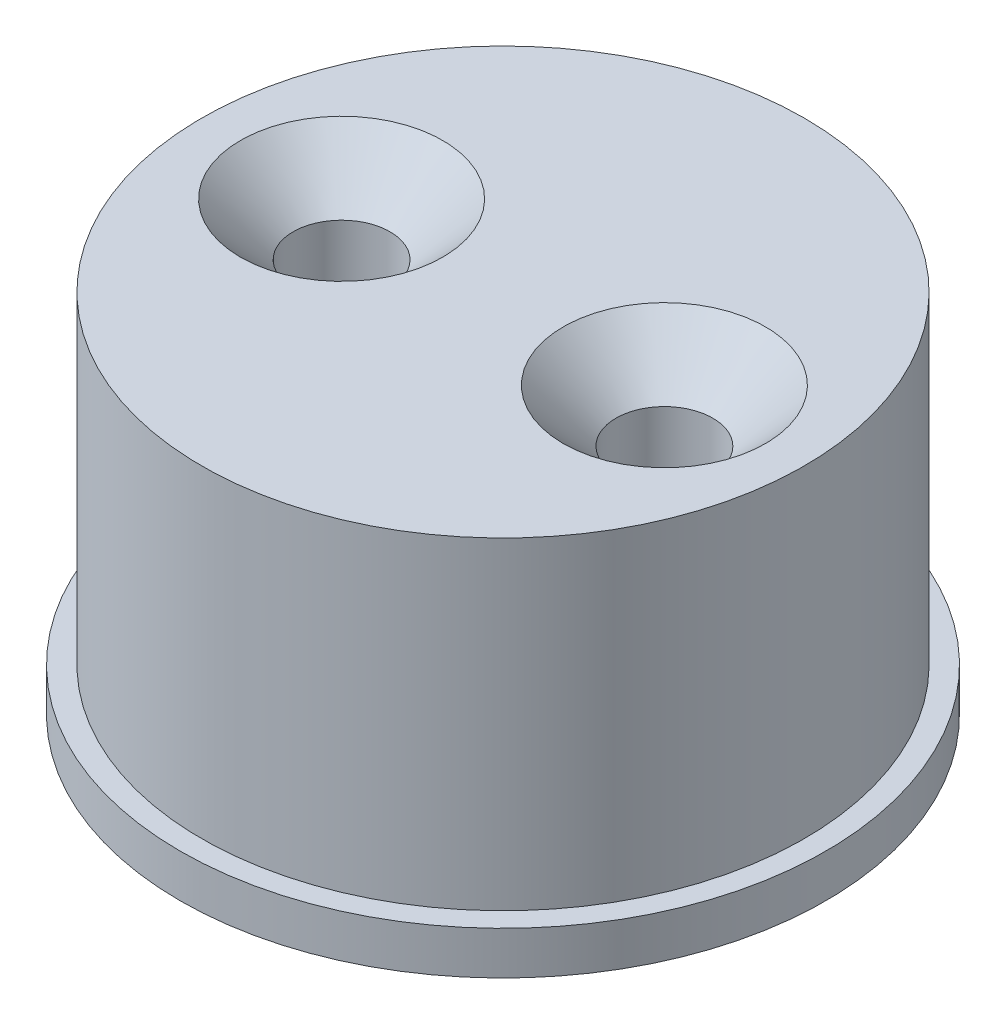
SolidWorks part; units mm, degrees
material "AISI 304"
ref_plane "정면" through (0, 0, 0) normal (0, 0, 1) x (1, 0, 0)
ref_plane "윗면" through (0, 0, 0) normal (0, 1, 0) x (1, 0, 0)
ref_plane "우측면" through (0, 0, 0) normal (1, 0, 0) x (0, 0, -1)
sketch "스케치1" plane through (0, 0, 0) normal (0, 0, 1) x (1, 0, 0)
  line L0 (0, 0) -> (0, 23.922) construction
  line L1 (0, 0) -> (-15, 0)
  line L2 (-15, 0) -> (-15, 2)
  line L3 (-15, 2) -> (-14, 2)
  line L4 (-14, 2) -> (-14, 17)
  line L5 (-14, 17) -> (0, 17)
  line L6 (0, 17) -> (0, 0)
  dimension "D1" = 30
  dimension "D2" = 28
  dimension "D3" = 2
  dimension "D4" = 15
revolve "회전1" add sketch "스케치1" angle 360 about L0
hole_wizard "M4 접시 머리 나사용 카운터싱크1" positions "스케치2" profile "스케치3" countersink size "M4" standard "ISO" end condition up to next
sketch "스케치2" plane through (0, 17, 0) normal (0, 1, 0) x (1, 0, 0)
  line L0 (-7.5, 0) -> (7.5, 0)
  circle A0 centre (0, 0) radius 14 construction
  point P0 (-7.5, 0)
  point P2 (7.5, 0)
  point P10 (0, 0)
  dimension "D1" = 15
sketch "스케치3" plane through (-7.5, 17, 0) normal (1, 0, 0) x (0, 0, 1)
  line L0 (0, 0) -> (0, 17)
  line L1 (0, 17) -> (2.25, 17)
  line L2 (2.25, 17) -> (2.25, 2.45)
  line L3 (2.25, 2.45) -> (4.7, 0)
  line L5 (4.7, 0) -> (0, 0)
  line L6 (-2.25, 2.45) -> (-4.7, 0) construction
  line L11 (0, -6.35) -> (0, 107.95) construction
  dimension "관통 구멍 지름" = 4.5
  dimension "관통 구멍 깊이" = 17
  dimension "표면 카운터싱크 지름" = 9.4
  dimension "표면 카운터싱크 각도" = 90
